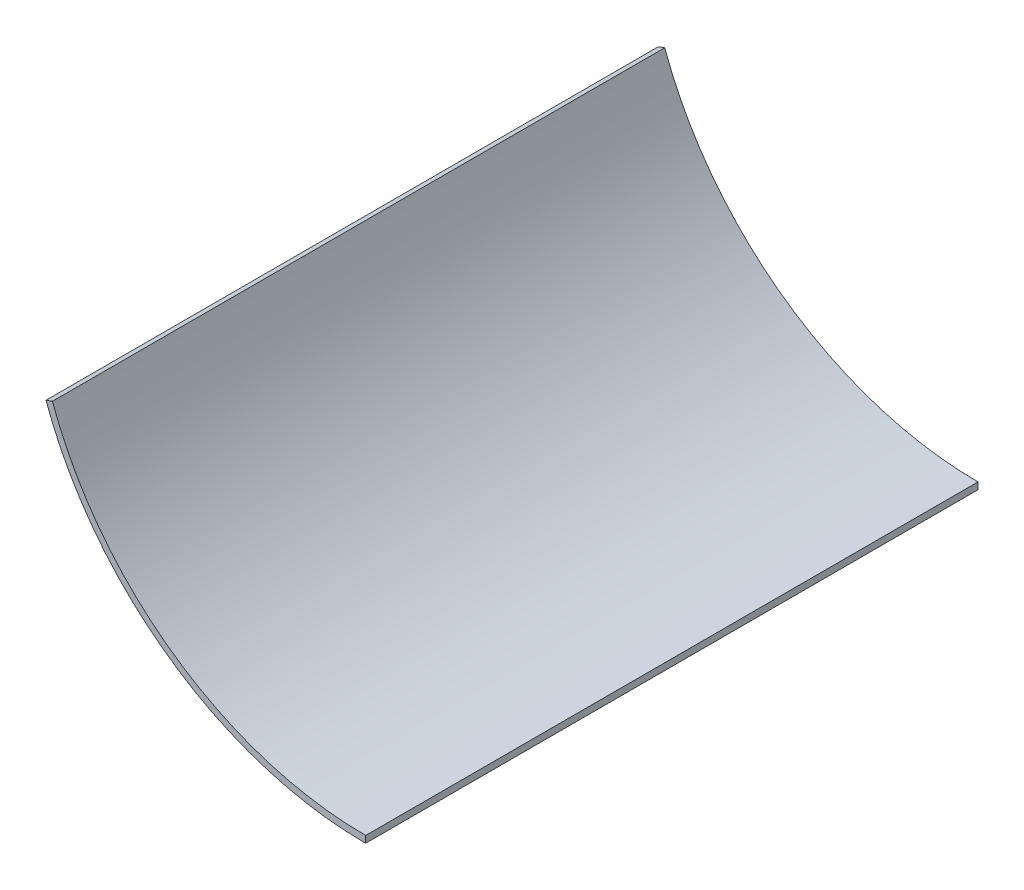
SolidWorks part; units mm, degrees
ref_plane "Płaszczyzna przednia" through (0, 0, 0) normal (0, 0, 1) x (1, 0, 0)
ref_plane "Płaszczyzna górna" through (0, 0, 0) normal (0, 1, 0) x (1, 0, 0)
ref_plane "Płaszczyzna prawa" through (0, 0, 0) normal (1, 0, 0) x (0, 0, -1)
sketch "Szkic1" plane through (0, 0, 0) normal (0, 0, 1) x (1, 0, 0)
  line L0 (-469.8463, -171.0101) -> (-460.4494, -167.5899)
  line L1 (0, -500) -> (0, -490)
  arc A0 (-469.8463, -171.0101) -> (0, -500) centre (0, 0) ccw
  arc A1 (-460.4494, -167.5899) -> (0, -490) centre (0, 0) ccw
  dimension "D1" = 490
  dimension "D2" = 500
  dimension "D3" = 10
  dimension "D4" = 70
extrude "Dodanie-wyciągnięcie1" add sketch "Szkic1" along normal blind 900
